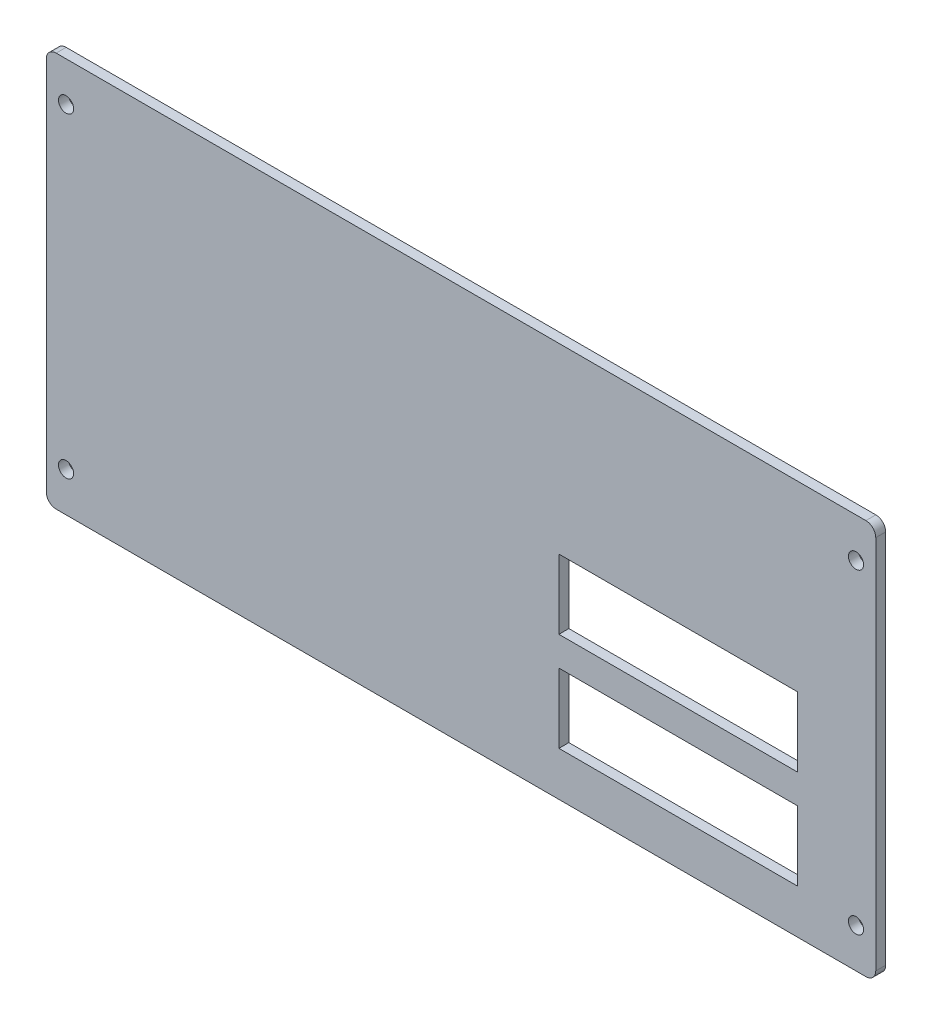
SolidWorks part; units mm, degrees
material "5052-H32"
ref_plane "Front Plane" through (0, 0, 0) normal (0, 0, 1) x (1, 0, 0)
ref_plane "Top Plane" through (0, 0, 0) normal (0, 1, 0) x (1, 0, 0)
ref_plane "Right Plane" through (0, 0, 0) normal (1, 0, 0) x (0, 0, -1)
sketch "Sketch1" plane through (0, 0, 0) normal (0, 0, 1) x (1, 0, 0)
  line L1 (-66.675, -31.75) -> (66.675, -31.75)
  line L2 (-66.675, -31.75) -> (-66.675, 31.75)
  line L3 (-66.675, 31.75) -> (66.675, 31.75)
  line L4 (66.675, -31.75) -> (66.675, 31.75)
  line L5 (-66.675, -31.75) -> (66.675, 31.75) construction
  line L6 (-66.675, 31.75) -> (66.675, -31.75) construction
  point P0 (0, 0)
  dimension "D1" = 133.35
  dimension "D2" = 63.5
extrude "Boss-Extrude1" add sketch "Sketch1" along normal blind 1.6002
sketch "Sketch2" plane through (0, 0, 0) normal (0, 0, -1) x (-1, 0, 0)
  line L0 (66.675, -31.75) -> (-66.675, -31.75) construction
  line L1 (-54.1147, -8.763) -> (-15.7353, -8.763)
  line L2 (-54.1147, -8.763) -> (-54.1147, 2.413)
  line L3 (-54.1147, 2.413) -> (-15.7353, 2.413)
  line L4 (-15.7353, -8.763) -> (-15.7353, 2.413)
  line L5 (-54.1147, -8.763) -> (-15.7353, 2.413) construction
  line L6 (-54.1147, 2.413) -> (-15.7353, -8.763) construction
  line L7 (-54.1147, -24.638) -> (-15.7353, -24.638)
  line L8 (-54.1147, -24.638) -> (-54.1147, -13.462)
  line L9 (-54.1147, -13.462) -> (-15.7353, -13.462)
  line L10 (-15.7353, -24.638) -> (-15.7353, -13.462)
  line L11 (-54.1147, -24.638) -> (-15.7353, -13.462) construction
  line L12 (-54.1147, -13.462) -> (-15.7353, -24.638) construction
  line L13 (-66.675, -31.75) -> (-66.675, 31.75) construction
  point P0 (-34.925, -3.175)
  point P6 (-34.925, -19.05)
  dimension "D1" = 38.3794
  dimension "D2" = 11.176
  dimension "D3" = 15.875
  dimension "D4" = 12.7
  dimension "D5" = 31.75
extrude "Cut-Extrude1" cut sketch "Sketch2" against normal through all
hole_wizard "#2 Clearance Hole1" positions "Sketch4" profile "Sketch3" hole size "#2" standard "Ansi Inch" end condition through all
sketch "Sketch4" plane through (0, 0, 0) normal (0, 0, -1) x (-1, 0, 0)
  line L1 (63.5, -25.4) -> (-63.5, -25.4) construction
  line L2 (63.5, -25.4) -> (63.5, 25.4) construction
  line L3 (63.5, 25.4) -> (-63.5, 25.4) construction
  line L4 (-63.5, -25.4) -> (-63.5, 25.4) construction
  line L5 (63.5, -25.4) -> (-63.5, 25.4) construction
  line L6 (63.5, 25.4) -> (-63.5, -25.4) construction
  line L7 (-66.675, 31.75) -> (66.675, 31.75) construction
  line L8 (-66.675, -31.75) -> (-66.675, 31.75) construction
  line L9 (66.675, 31.75) -> (66.675, -31.75) construction
  line L10 (66.675, -31.75) -> (-66.675, -31.75) construction
  point P0 (-63.5, 25.4)
  point P1 (63.5, 25.4)
  point P3 (63.5, -25.4)
  point P5 (-63.5, -25.4)
  dimension "D1" = 6.35
  dimension "D2" = 3.175
  dimension "D3" = 3.175
  dimension "D4" = 6.35
sketch "Sketch3" plane through (63.5, 25.4, 0) normal (1, 0, 0) x (0, 1, 0)
  line L0 (0, 0) -> (0, 1.6002)
  line L1 (0, 1.6002) -> (1.2192, 1.6002)
  line L2 (1.2192, 1.6002) -> (1.2192, 0)
  line L5 (1.2192, 0) -> (0, 0)
  line L11 (0, -6.35) -> (0, 107.95) construction
  dimension "Thru Hole Dia." = 2.4384
  dimension "Thru Hole Depth" = 1.6002
fillet "Fillet1" radius 1.5875 4 edges at (-66.675, -31.75, 0.8001) (66.675, -31.75, 0.8001) (66.675, 31.75, 0.8001) (-66.675, 31.75, 0.8001)
sketch "Sketch5" plane through (0, 0, 0) normal (0, 0, -1) x (-1, 0, 0)
  line L0 (-54.1147, -8.763) -> (-15.7353, -8.763) construction
  line L1 (-54.1147, -24.638) -> (-15.7353, -24.638) construction
  line L2 (-15.7353, -8.763) -> (-15.7353, 2.413) construction
  text T0 "PWR IN"
  text T1 "PWR OUT"
  dimension "D1" = 3.81
  dimension "D2" = 3.81
  dimension "D3" = 6.35
extrude "Cut-Extrude2" cut sketch "Sketch5" against normal blind 0.2286
